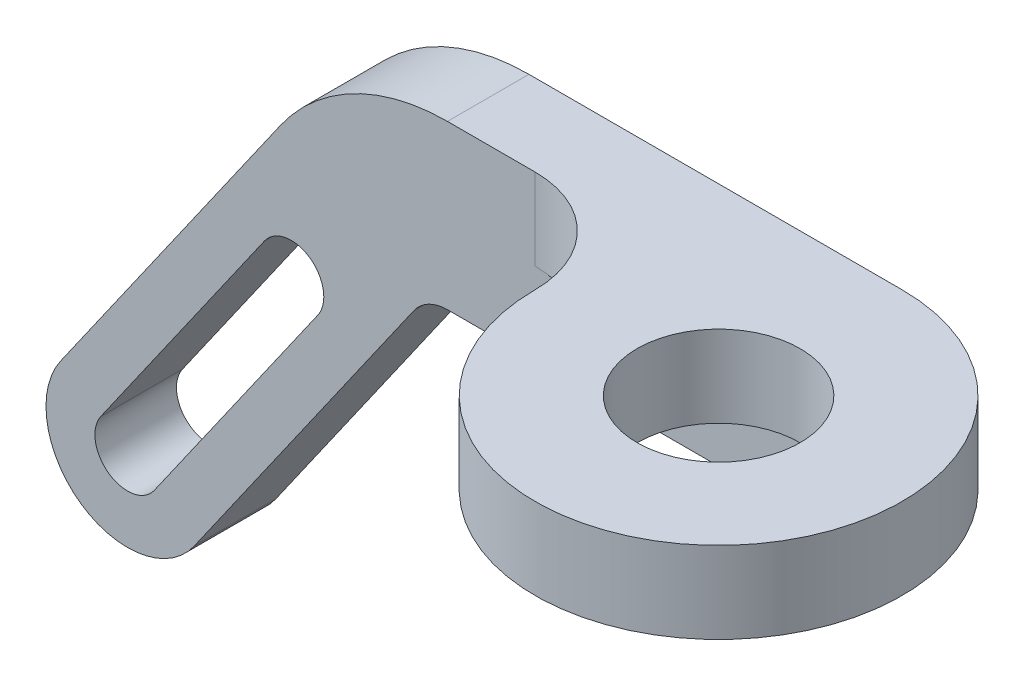
SolidWorks part; units mm, degrees
ref_plane "Plano frontal" through (0, 0, 0) normal (0, 0, 1) x (1, 0, 0)
ref_plane "Plano superior" through (0, 0, 0) normal (0, 1, 0) x (1, 0, 0)
ref_plane "Plano direito" through (0, 0, 0) normal (1, 0, 0) x (0, 0, -1)
sketch "Sketch1" plane through (0, 0, 0) normal (0, 0, 1) x (1, 0, 0)
  line L0 (11.4985, 11.0062) -> (-15.4514, -27.4824)
  line L1 (-4.8845, 22.4777) -> (-31.8345, -16.0109)
  line L2 (15.5943, 33.1383) -> (61.3571, 33.1383)
  line L3 (15.5943, 13.1383) -> (61.3571, 13.1383)
  line L4 (-31.8345, -16.0109) -> (-12.69, -29.416) construction
  line L5 (61.3571, 55.7241) -> (61.3571, -2.5036) construction
  line L6 (61.3571, 33.1383) -> (61.3571, 13.1383)
  line L7 (-26.9196, -19.4523) -> (-6.8444, 9.218)
  line L8 (-20.3663, -24.0409) -> (-0.2912, 4.6294)
  arc A0 (-31.8345, -16.0109) -> (-15.4514, -27.4824) centre (-23.6429, -21.7466) ccw
  arc A1 (15.5943, 33.1383) -> (-4.8845, 22.4777) centre (15.5943, 8.1383) ccw
  arc A2 (15.5943, 13.1383) -> (11.4985, 11.0062) centre (15.5943, 8.1383) ccw
  arc A3 (-26.9196, -19.4523) -> (-20.3663, -24.0409) centre (-23.6429, -21.7466) ccw
  arc A4 (-0.2912, 4.6294) -> (-6.8444, 9.218) centre (-3.5678, 6.9237) ccw
  point P12 (2.5801, 33.1383)
  dimension "D4" = 10
  dimension "D6" = 60
  dimension "D7" = 5
  dimension "D8" = 4
  dimension "D9" = 6
  dimension "D10" = 35
  dimension "D11" = 25
  dimension "D1" = 125
  dimension "D2" = 20
  dimension "D3" = 20
  dimension "D5" = 85
extrude "Extrude1" add sketch "Sketch1" along normal mid plane 10
sketch "Sketch2" plane through (0, 33.1383, 0) normal (0, 1, 0) x (1, 0, 0)
  line L0 (61.3571, 5) -> (61.3571, -63.357) construction
  line L1 (61.3571, 5) -> (15.5943, 5) construction
  line L2 (61.3571, 5) -> (15.5943, 5)
  line L3 (15.5943, 5) -> (15.5943, -5)
  line L4 (15.5943, -5) -> (26.3571, -5)
  line L5 (61.3571, -5) -> (15.5943, -5) construction
  line L6 (61.3571, -17.5) -> (-9.0109, -17.5) construction
  arc A0 (38.8571, -17.5) -> (61.3571, 5) centre (61.3571, -17.5) ccw
  circle A1 centre (61.3571, -17.5) radius 10
  arc A2 (26.3571, -5) -> (38.8571, -17.5) centre (26.3571, -17.5) cw
  dimension "D1" = 45
  dimension "D2" = 20
extrude "Extrude2" add sketch "Sketch2" against normal blind 10
sketch "Esboço1" plane through (61.3571, 0, 0) normal (1, 0, 0) x (0, 0, -1)
  line L0 (-5, 23.1383) -> (5, 13.1383) construction
  line L2 (-5, 13.1383) -> (5, 23.1383) construction
  point P9 (0, 18.1383)
hole_wizard "Broca de rosquear para tarraxa de M2.2x0.451" positions "3DSketch2" profile "Esboço3" hole size "M2.2x0.45" standard "Métrico Ansi"
sketch3d "3DSketch2"
  point P0 (61.3571, 18.1383, 0)
sketch "Esboço3" plane through (61.3571, 18.1383, 0) normal (0, 1, 0) x (0, 0, -1)
  line L0 (0, 0) -> (0, 5.5258)
  line L1 (0, 5.5258) -> (0.875, 5)
  line L2 (0.875, 5) -> (0.875, 0)
  line L5 (0.875, 0) -> (0, 0)
  line L10 (0, 5.5258) -> (-0.875, 5) construction
  line L11 (0, -6.35) -> (0, 107.95) construction
  dimension "Hole Dia." = 1.75
  dimension "Hole Depth" = 5
  dimension "Drill Angle" = 118
